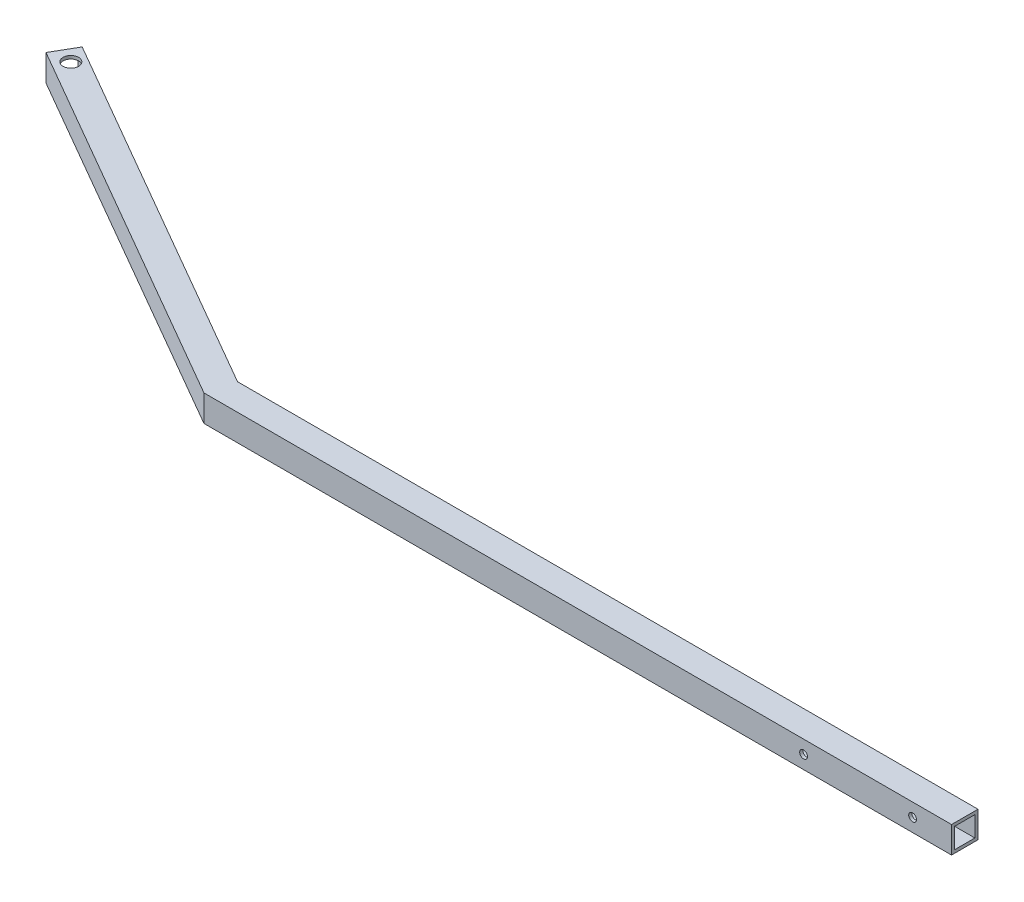
SolidWorks part; units mm, degrees
material "AISI 1015 Steel, Cold Drawn (SS)"
ref_plane "Front Plane" through (0, 0, 0) normal (0, 0, 1) x (1, 0, 0)
ref_plane "Top Plane" through (0, 0, 0) normal (0, 1, 0) x (1, 0, 0)
ref_plane "Right Plane" through (0, 0, 0) normal (1, 0, 0) x (0, 0, -1)
other "Configuration Table"
sketch "Sketch1" plane through (0, 0, 0) normal (0, 1, 0) x (1, 0, 0)
  line L0 (0, 0) -> (-609.6, 0)
  line L1 (-609.6, 0) -> (-914.4, 175.9764)
  line L2 (0, 21.59) -> (-603.815, 21.59)
  line L3 (-603.815, 21.59) -> (-903.605, 194.6739)
  line L4 (-903.605, 194.6739) -> (-914.4, 175.9764)
  line L5 (0, 21.59) -> (0, 0)
  dimension "D1" = 30
  dimension "D3" = 609.6
  dimension "D4" = 304.8
  dimension "D2" = 21.59
extrude "Boss-Extrude1" add sketch "Sketch1" against normal blind 21.59
shell "Shell3" thickness 2.54
sketch "Sketch2" plane through (0, 0, 0) normal (0, 0, 1) x (1, 0, 0)
  line L2 (0, -21.59) -> (0, 0) construction
  line L3 (0, -10.7913) -> (-187.7371, -10.7913) construction
  circle A2 centre (-120.65, -10.7913) radius 3.175
  circle A3 centre (-31.75, -10.7913) radius 3.175
  dimension "D1" = 6.35
  dimension "D2" = 88.9
  dimension "D3" = 31.75
extrude "PIN HOLES" cut sketch "Sketch2" against normal through all
sketch "Sketch3" plane through (0, 0, 0) normal (0, 1, 0) x (1, 0, 0)
  line L3 (-603.815, 21.59) -> (-903.605, 194.6739) construction
  line L5 (-903.605, 194.6739) -> (-914.4, 175.9764) construction
  circle A0 centre (-897.6865, 179.525) radius 6.35
  dimension "D3" = 12.7
  dimension "D1" = 10.16
  dimension "D2" = 12.7
extrude "TOW HITCH ADAPTOR HOLE" cut sketch "Sketch3" against normal through all
equation "\"A\"= 3"
equation "\"B\"= 1"
